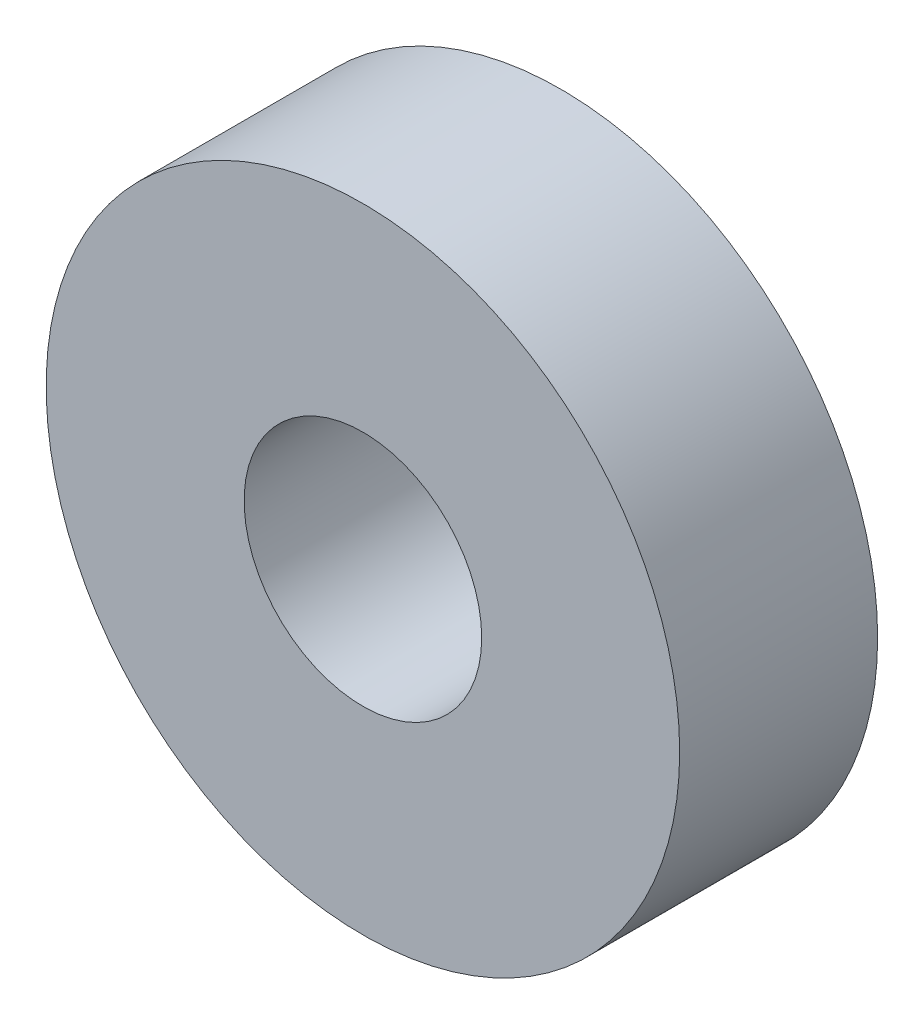
SolidWorks part; units mm, degrees
ref_plane "Plan de face" through (0, 0, 0) normal (0, 0, 1) x (1, 0, 0)
ref_plane "Plan de dessus" through (0, 0, 0) normal (0, 1, 0) x (1, 0, 0)
ref_plane "Plan de droite" through (0, 0, 0) normal (1, 0, 0) x (0, 0, -1)
sketch "Esquisse1" plane through (0, 0, 0) normal (0, 0, 1) x (1, 0, 0)
  circle A0 centre (0, 0) radius 8
  circle A1 centre (0, 0) radius 3
  point P4 (0, 0)
  point P7 (0, 0)
  dimension "D1" = 16
  dimension "D2" = 6
extrude "Boss.-Extru.1" add sketch "Esquisse1" along normal blind 5
